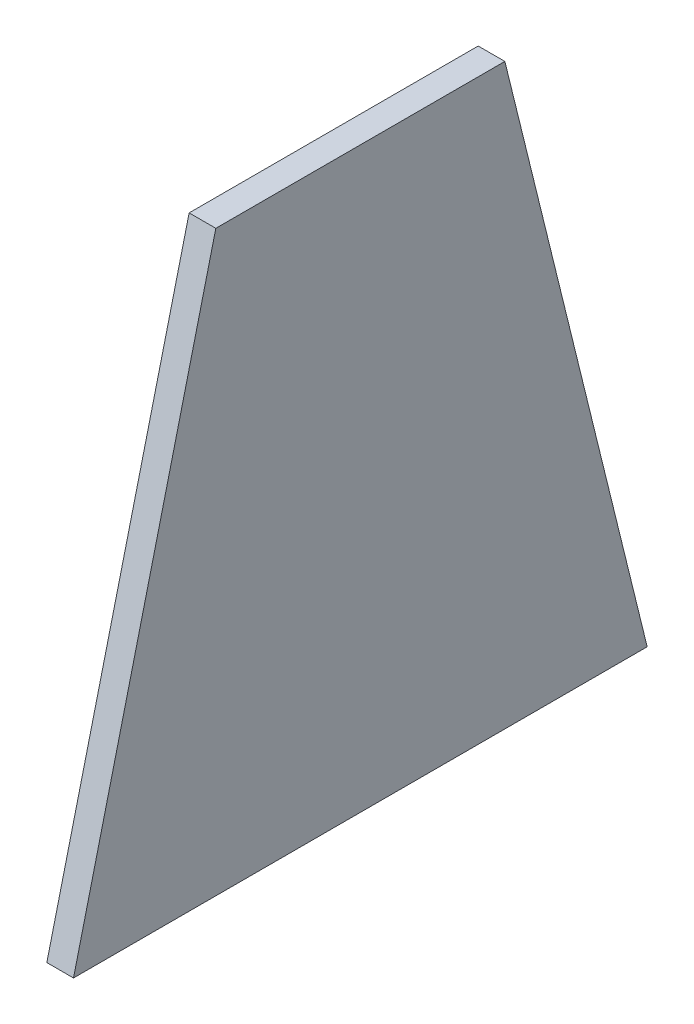
SolidWorks part; units mm, degrees
ref_plane "Alzado" through (0, 0, 0) normal (0, 0, 1) x (1, 0, 0)
ref_plane "Planta" through (0, 0, 0) normal (0, 1, 0) x (1, 0, 0)
ref_plane "Vista lateral" through (0, 0, 0) normal (1, 0, 0) x (0, 0, -1)
sketch "Croquis2" plane through (0, 0, 0) normal (1, 0, 0) x (0, 0, -1)
  line L24 (-15.1058, 33.4383) -> (17.3942, 33.4383)
  line L25 (17.3942, 33.4383) -> (33.3942, -31.5617)
  line L26 (33.3942, -31.5617) -> (-31.1058, -31.5617)
  line L27 (-31.1058, -31.5617) -> (-15.1058, 33.4383)
extrude "Saliente-Extruir1" add sketch "Croquis2" along normal blind 3
